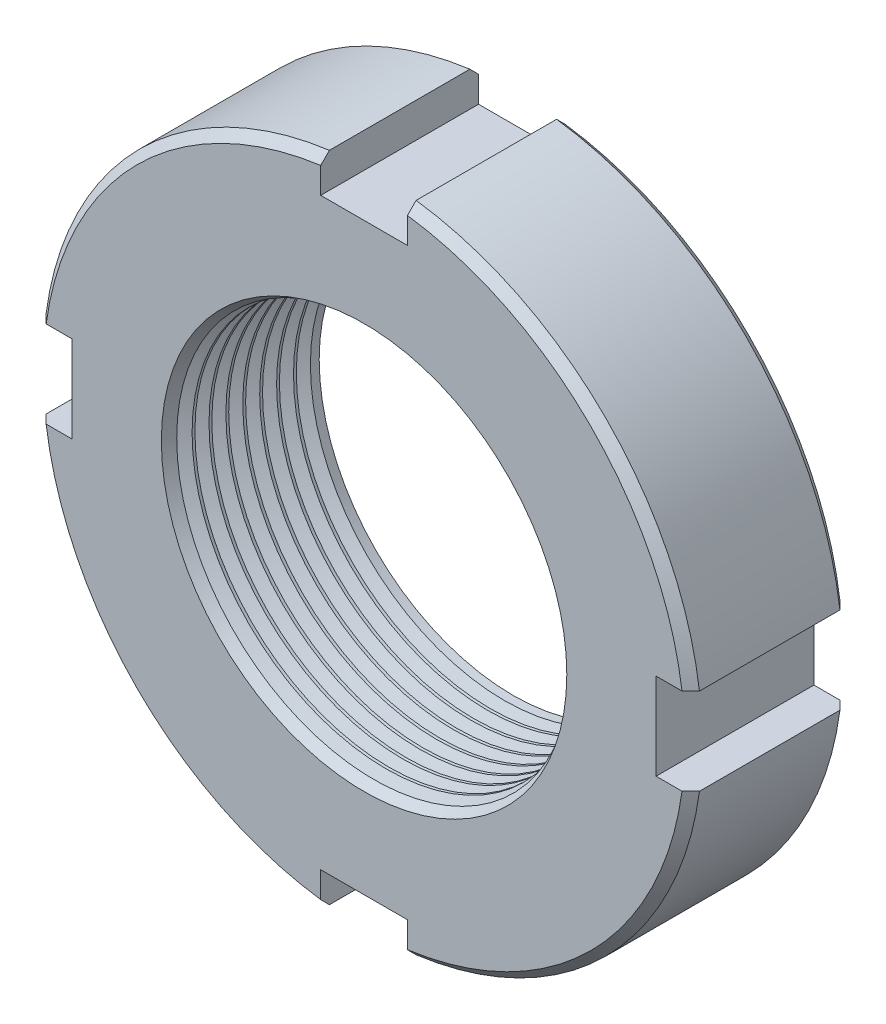
SolidWorks part; units mm, degrees
ref_plane "Front" through (0, 0, 0) normal (0, 0, 1) x (1, 0, 0)
ref_plane "Top" through (0, 0, 0) normal (0, 1, 0) x (1, 0, 0)
ref_plane "Right" through (0, 0, 0) normal (1, 0, 0) x (0, 0, -1)
sketch "Sketch2" plane through (0, 0, 0) normal (0, 0, 1) x (1, 0, 0)
  circle A0 centre (0, 0) radius 19
  dimension "dk" = 38
extrude "BaseNut" add sketch "Sketch2" against normal blind 9.1
chamfer "Chamfer1" distance 0.5 angle 45 2 edges at (19, 0, -9.1) (19, 0, 0)
sketch "Sketch3" plane through (-17.5617, 31.6827, 0) normal (0, 0, 1) x (1, 0, 0)
  circle A0 centre (17.5617, -31.6827) radius 11.188
  circle A1 centre (17.5617, -31.6827) radius 18.5 construction
  dimension "D1" = 22.376
extrude "Hole" cut sketch "Sketch3" against normal through all
cosmetic thread "ThreadCosmetic1" [suppressed] parameters "D2"=24
chamfer "EndChamfer" distance 0.5 angle 60 2 edges at (11.188, 0, 0) (11.188, 0, -9.1)
sketch "Sketch4" plane through (-28.8484, 49.2663, 0) normal (0, 0, 1) x (1, 0, 0)
  line L0 (28.8484, 68.6571) -> (28.8484, -68.9081) construction
  line L2 (26.3484, -30.4315) -> (31.3484, -30.4315) construction
  line L3 (26.3484, -30.4315) -> (26.3484, -32.4315)
  line L4 (26.3484, -32.4315) -> (31.3484, -32.4315)
  line L5 (31.3484, -30.4315) -> (31.3484, -32.4315)
  arc A1 (31.3484, -30.4315) -> (26.3484, -30.4315) centre (28.8484, -49.2663) ccw
  circle A2 centre (28.8484, -49.2663) radius 19 construction
  dimension "n" = 5
  dimension "t" = 2
extrude "SlotCut" cut sketch "Sketch4" against normal through all
pattern_circular "SlotPat" count 4 over 360 about axis through (0, 0, 0) along (0, 0, 1) of "SlotCut"
sketch "Sketch5" plane through (0, 0, 0) normal (0, 1, 0) x (1, 0, 0)
  line L0 (10.376, 1.272) -> (10.376, 0.46)
  line L1 (10.376, 0.46) -> (11.188, 0.46)
  line L2 (11.188, 0.46) -> (11.8912, 0.866)
  line L3 (11.8912, 0.866) -> (11.188, 1.272)
  line L4 (11.188, 1.272) -> (10.376, 1.272)
  line L5 (0, 37.3018) -> (0, -33.5096) construction
  line L9 (11.188, 0.866) -> (-11.188, 0.866) construction
  dimension "D1" = 0.812
  dimension "D2" = 22.376
revolve "Cut-Revolve10" cut sketch "Sketch5" angle 360 about L5
pattern_linear "LPattern10" count 8 spacing 0.9744 along (0, 0, -1) of "Cut-Revolve10"
equation "\"D1@Sketch5\" =  ( \"D2@ThreadCosmetic1\" - \"D1@Sketch3\" )  / 2"
equation "\"D3@LPattern10\" = \"D1@Sketch5\" * 1.2"
equation "\"D1@LPattern10\" = \"m@BaseNut\" / \"D3@LPattern10\"-1"
equation "\"D2@Sketch5\" = \"D1@Sketch3\""
